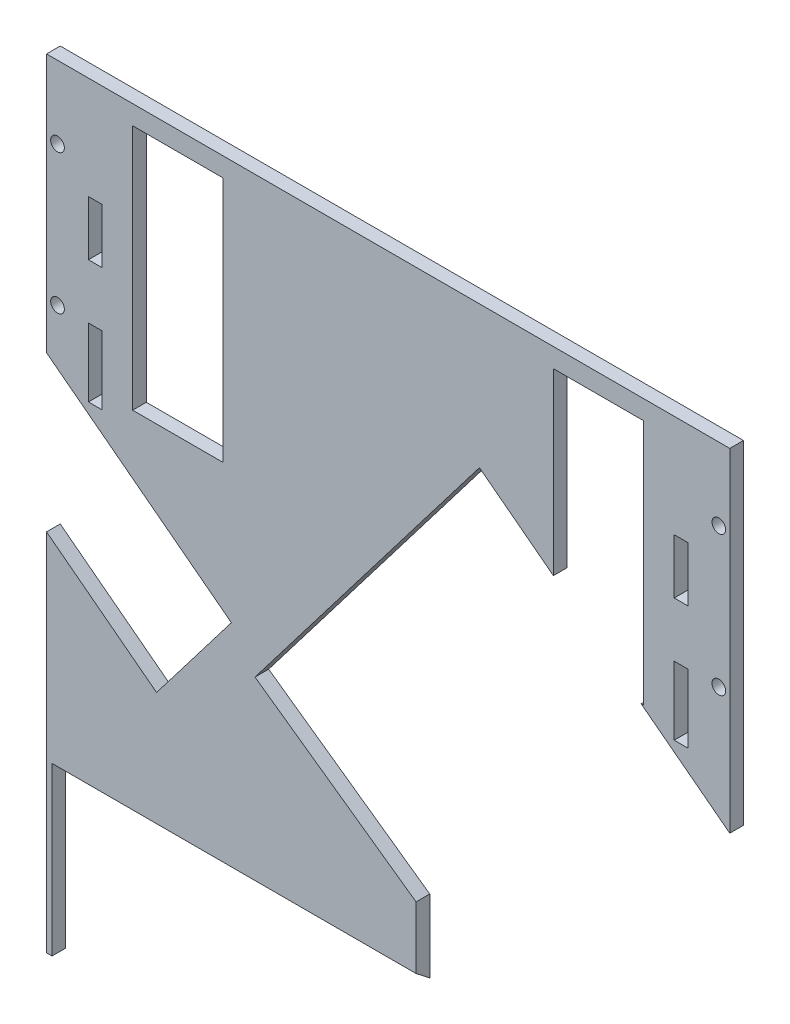
SolidWorks part; units mm, degrees
ref_plane "Front Plane" through (0, 0, 0) normal (0, 0, 1) x (1, 0, 0)
ref_plane "Top Plane" through (0, 0, 0) normal (0, 1, 0) x (1, 0, 0)
ref_plane "Right Plane" through (0, 0, 0) normal (1, 0, 0) x (0, 0, -1)
sketch "Sketch1" plane through (0, 0, 0) normal (0, 0, 1) x (1, 0, 0)
  line L0 (124.8, 0) -> (124.8, -284.42) construction
  line L1 (0, 0) -> (249.6, 0)
  line L2 (0, 0) -> (0, -284.42)
  line L3 (0, -284.42) -> (249.6, -284.42)
  line L4 (249.6, 0) -> (249.6, -284.42)
  line L9 (185.16, -7) -> (218.16, -7)
  line L10 (185.16, -7) -> (185.16, -97)
  line L11 (185.16, -97) -> (218.16, -97)
  line L12 (218.16, -7) -> (218.16, -97)
  line L52 (204.16, -7) -> (204.16, -97) construction
  line L53 (194.16, -7) -> (214.16, -7) construction
  line L54 (194.16, -7) -> (194.16, -97) construction
  line L55 (194.16, -97) -> (214.16, -97) construction
  line L56 (214.16, -7) -> (214.16, -97) construction
  line L102 (245.6, -26.5) -> (245.6, -77.5) construction
  line L103 (218.16, -52) -> (245.6, -52) construction
  line L134 (31.44, -52) -> (4, -52) construction
  line L135 (4, -26.5) -> (4, -77.5) construction
  line L139 (35.44, -7) -> (35.44, -97) construction
  line L140 (55.44, -97) -> (35.44, -97) construction
  line L141 (55.44, -7) -> (55.44, -97) construction
  line L142 (55.44, -7) -> (35.44, -7) construction
  line L143 (45.44, -7) -> (45.44, -97) construction
  line L154 (31.44, -7) -> (31.44, -97)
  line L155 (64.44, -97) -> (31.44, -97)
  line L156 (64.44, -7) -> (64.44, -97)
  line L157 (64.44, -7) -> (31.44, -7)
  circle A84 centre (245.6, -26.5) radius 2.5
  circle A85 centre (245.6, -77.5) radius 2.5
  circle A236 centre (4, -77.5) radius 2.5
  circle A237 centre (4, -26.5) radius 2.5
  dimension "D5" = 20
  dimension "D15" = 5
  dimension "D16" = 5
  dimension "D1" = 249.6
  dimension "D2" = 284.42
  dimension "D3" = 4
  dimension "D4" = 90
  dimension "D6" = 90
  dimension "D7" = 9
  dimension "D8" = 7
  dimension "D14" = 89.36
  dimension "D17" = 25.5
  dimension "D18" = 4
extrude "Boss-Extrude1" add sketch "Sketch1" along normal blind 5
sketch "Sketch2" plane through (0, 0, 5) normal (0, 0, 1) x (1, 0, 0)
  line L0 (-12.0438, -116.1701) -> (14.8299, 12.0438) construction
  line L1 (357.917, -193.7139) -> (384.7906, -65.5) construction
  line L2 (-12.0438, -116.1701) -> (357.917, -193.7139) construction
  line L3 (28.6688, 50.2813) -> (25.735, 46.2325) construction
  line L4 (25.735, 46.2325) -> (79.8591, 7.0134) construction
  line L5 (89.8056, 5.9807) -> (28.6688, 50.2813) construction
  line L6 (14.8299, 12.0438) -> (384.7906, -65.5) construction
  line L7 (14.2144, 9.1076) -> (384.1752, -68.4362) construction
  line L8 (-11.4283, -113.2339) -> (358.5324, -190.7777) construction
  line L9 (28.6688, 50.2813) -> (31.6026, 54.33) construction
  line L10 (31.6026, 54.33) -> (85.7267, 15.111) construction
  line L11 (236.1909, -165.1349) -> (261.8337, -42.7934) construction
  line L12 (126.6708, -78.3214) -> (249.0123, -103.9642) construction
  line L13 (113.8494, -139.4922) -> (139.4922, -17.1506) construction
  line L14 (249.6, 0) -> (0, 0) construction
  line L15 (0, 0) -> (0, -284.42) construction
  circle A0 centre (65.5, -65.5) radius 62.5 construction
  circle A1 centre (310.183, -116.7856) radius 62.5 construction
  circle A2 centre (65.5, -65.5) radius 65.5 construction
  circle A3 centre (187.8415, -91.1428) radius 62.5 construction
  circle A4 centre (89.8056, 5.9807) radius 75.5 construction
  circle A5 centre (89.8056, 5.9807) radius 2.5 construction
  circle A6 centre (69.5617, 20.6497) radius 1.5 construction
  arc A7 (79.8591, 7.0134) -> (85.7267, 15.111) centre (89.8056, 5.9807) ccw construction
  dimension "D1" = 125
  dimension "D2" = 125
  dimension "D3" = 5
  dimension "D6" = 3
  dimension "D7" = 10
  dimension "D10" = 125
  dimension "D8" = 3
  dimension "D4" = 5
  dimension "D5" = 25
  dimension "D9" = 5
ref_plane "Plane1"
sketch "Sketch4" plane through (0, -141.1875, 110.3078) normal (0, 0.788, -0.6157) x (1, 0, 0)
  line L0 (2, 206.4003) -> (135, 206.4003)
  line L1 (2, 206.4003) -> (2, -38.0664)
  line L2 (135, 206.4003) -> (135, -38.0664)
  line L3 (2, -38.0664) -> (135, -38.0664)
  line L4 (0, 253.2196) -> (0, 43.3406) construction
  line L5 (2, -22.0114) -> (2, 231.4168) construction
  line L6 (135, 253.2196) -> (135, 43.3406) construction
extrude "Cut-Extrude2" cut sketch "Sketch4" against normal through all
sketch "Sketch5" plane through (0, 0, 5) normal (0, 0, 1) x (1, 0, 0)
  line L0 (76.1492, -159.0843) -> (158.1494, -51.8418)
  line L1 (135, -284.42) -> (207.3188, -339.7167)
  line L2 (158.1494, -51.8418) -> (328.0831, -181.7773)
  line L3 (207.3188, -339.7167) -> (328.0831, -181.7773)
  line L4 (79.1862, -155.1124) -> (155.1124, -55.8138) construction
  line L5 (76.1492, -159.0843) -> (135, -200.789)
  line L6 (54.8789, 27.1214) -> (359.1299, -205.5164) construction
  line L7 (135, -200.789) -> (135, -284.42)
  line L8 (135, -284.42) -> (135, -223.463) construction
extrude "Cut-Extrude3" cut sketch "Sketch5" against normal through all
sketch "Sketch6" plane through (0, 0, 5) normal (0, 0, 1) x (1, 0, 0)
  line L0 (0, -94.5647) -> (67.5231, -146.1945)
  line L1 (0, -94.5647) -> (-27.3334, -130.3122)
  line L2 (67.5231, -146.1945) -> (40.1896, -181.942)
  line L3 (-27.3334, -130.3122) -> (40.1896, -181.942)
  line L4 (0, 0) -> (0, -284.42) construction
  line L5 (-24.0843, -76.1492) -> (280.1666, -308.787) construction
  dimension "D1" = 85
  dimension "D2" = 45
extrude "Cut-Extrude4" cut sketch "Sketch6" against normal through all
sketch "Sketch7" plane through (0, 0, 5) normal (0, 0, 1) x (1, 0, 0)
  line L0 (124.8, 45.2798) -> (124.8, -137.1886) construction
  line L18 (15.2882, -37.4779) -> (20.2882, -37.4779)
  line L19 (15.2882, -37.4779) -> (15.2882, -57.4779)
  line L23 (15.2882, -57.4779) -> (20.2882, -57.4779)
  line L24 (20.2882, -37.4779) -> (20.2882, -57.4779)
  line L25 (229.3118, -37.4779) -> (234.3118, -37.4779)
  line L26 (229.3118, -37.4779) -> (229.3118, -57.4779)
  line L27 (229.3118, -57.4779) -> (234.3118, -57.4779)
  line L28 (234.3118, -37.4779) -> (234.3118, -57.4779)
  line L29 (15.2882, -77.4779) -> (20.2882, -77.4779)
  line L30 (15.2882, -77.4779) -> (15.2882, -102.4779)
  line L31 (15.2882, -102.4779) -> (20.2882, -102.4779)
  line L32 (20.2882, -77.4779) -> (20.2882, -102.4779)
  line L33 (229.3118, -77.4779) -> (234.3118, -77.4779)
  line L34 (229.3118, -77.4779) -> (229.3118, -102.4779)
  line L35 (229.3118, -102.4779) -> (234.3118, -102.4779)
  line L36 (234.3118, -77.4779) -> (234.3118, -102.4779)
  line L37 (17.7882, -37.4779) -> (17.7882, -111.359) construction
  line L38 (231.8118, -37.4779) -> (231.8118, -111.6165) construction
  line L39 (0, 0) -> (0, -94.5647) construction
  line L40 (249.6, -121.7672) -> (249.6, 0) construction
  line L42 (249.6, -121.7672) -> (217.2087, -97) construction
  line L43 (67.5231, -146.1945) -> (0, -94.5647) construction
  dimension "D1" = 5
  dimension "D2" = 20
  dimension "D3" = 5
  dimension "D4" = 20
  dimension "D5" = 5
  dimension "D6" = 25
  dimension "D7" = 5
  dimension "D8" = 25
  dimension "D9" = 20
  dimension "D10" = 20
  dimension "D11" = 3
  dimension "D12" = 3
extrude "Cut-Extrude5" cut sketch "Sketch7" against normal through all
